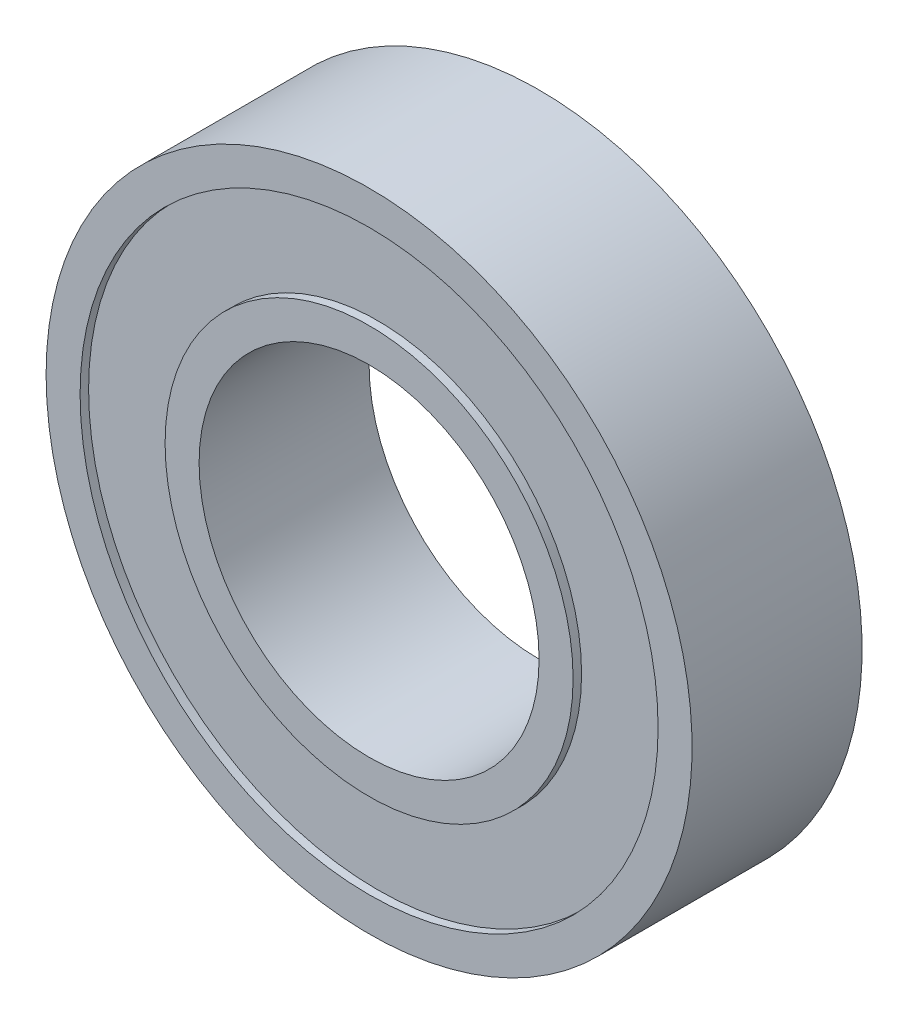
SolidWorks part; units mm, degrees
material "AISI 4130 Steel, annealed at 865C"
ref_plane "Front Plane" through (0, 0, 0) normal (0, 0, 1) x (1, 0, 0)
ref_plane "Top Plane" through (0, 0, 0) normal (0, 1, 0) x (1, 0, 0)
ref_plane "Right Plane" through (0, 0, 0) normal (1, 0, 0) x (0, 0, -1)
sketch "Sketch1" plane through (0, 0, 0) normal (0, 1, 0) x (1, 0, 0)
  line L0 (5, -2.5) -> (6, -2.5)
  line L1 (6, -2.5) -> (6, -2.25)
  line L2 (6, -2.25) -> (8.5, -2.25)
  line L3 (8.5, -2.25) -> (8.5, -2.5)
  line L4 (8.5, -2.5) -> (9.5, -2.5)
  line L7 (9.5, -2.5) -> (9.5, 2.5)
  line L8 (9.5, 2.5) -> (8.5, 2.5)
  line L9 (8.5, 2.5) -> (8.5, 2.25)
  line L10 (8.5, 2.25) -> (6, 2.25)
  line L11 (6, 2.25) -> (6, 2.5)
  line L12 (6, 2.5) -> (5, 2.5)
  line L13 (5, 2.5) -> (5, -2.5)
  line L14 (0, 2.5) -> (0, -2.5) construction
  dimension "D1" = 5
  dimension "D2" = 1
  dimension "D3" = 9.5
  dimension "D4" = 4.5
  dimension "D5" = 1
  dimension "D8" = 5
revolve "Revolve1" add sketch "Sketch1" angle 360 about L14
